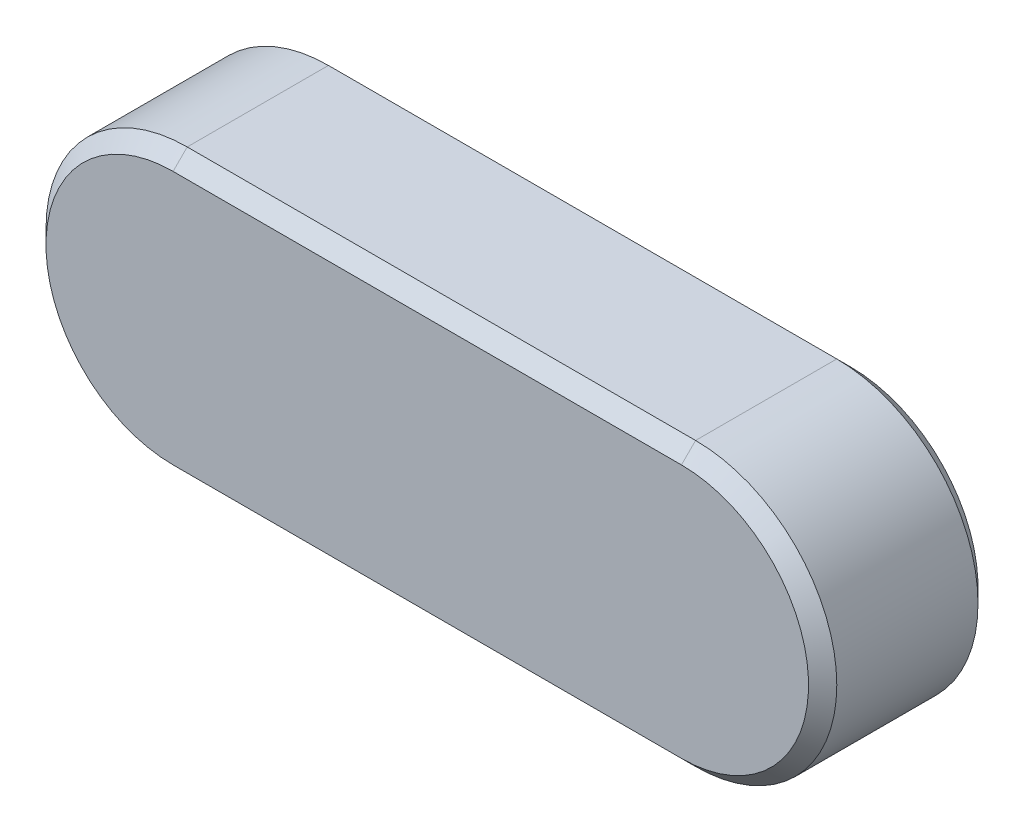
SolidWorks part; units mm, degrees
ref_plane "Front" through (0, 0, 0) normal (0, 0, 1) x (1, 0, 0)
ref_plane "Top" through (0, 0, 0) normal (0, 1, 0) x (1, 0, 0)
ref_plane "Right" through (0, 0, 0) normal (1, 0, 0) x (0, 0, -1)
sketch "Sketch1" plane through (0, 0, 0) normal (0, 0, 1) x (1, 0, 0)
  line L0 (0, 2.5) -> (-9, 2.5)
  line L1 (-9, -2.5) -> (0, -2.5)
  arc A0 (-9, 2.5) -> (-9, -2.5) centre (-9, 0) ccw
  arc A1 (0, -2.5) -> (0, 2.5) centre (0, 0) ccw
  dimension "b" = 5
  dimension "l" = 14
extrude "Extrude1" add sketch "Sketch1" along normal blind 3
sketch "Sketch2" plane through (0, 0, 0) normal (0, 0, 1) x (1, 0, 0)
  line L0 (0, 2.5) -> (-9, 2.5) construction
  line L1 (-11.5, 2.5) -> (2.5, 2.5)
  line L2 (-11.5, 2.5) -> (-11.5, -2.5)
  line L3 (-11.5, -2.5) -> (2.5, -2.5)
  line L4 (2.5, 2.5) -> (2.5, -2.5)
  line L5 (-9, -2.5) -> (0, -2.5) construction
  arc A0 (-9, 2.5) -> (-9, -2.5) centre (-9, 0) ccw construction
  arc A1 (0, -2.5) -> (0, 2.5) centre (0, 0) ccw construction
extrude "Extrude2" [suppressed] add sketch "Sketch2" along normal blind 3
sketch "Sketch3" plane through (0, 0, 0) normal (0, 0, 1) x (1, 0, 0)
  line L0 (-9, -2.5) -> (0, -2.5) construction
  line L1 (-9, -2.5) -> (2.5, -2.5)
  line L3 (-9, 2.5) -> (2.5, 2.5)
  line L4 (2.5, -2.5) -> (2.5, 2.5)
  arc A1 (-9, 2.5) -> (-9, -2.5) centre (-9, 0) ccw
  arc A2 (0, -2.5) -> (0, 2.5) centre (0, 0) ccw construction
  arc A3 (-9, 2.5) -> (-9, -2.5) centre (-9, 0) ccw construction
extrude "Extrude3" [suppressed] add sketch "Sketch3" along normal blind 3
chamfer "Chamfer1" distance 0.25 angle 45 8 edges at (-4.5, 2.5, 0) (-4.5, -2.5, 0) (-4.5, 2.5, 3) (-4.5, -2.5, 3) (-11.5, 0, 0) (-11.5, 0, 3) (2.5, 0, 0) (2.5, 0, 3)
equation "\"D1@Extrude2\" = \"h@Extrude1\""
equation "\"D1@Extrude3\" = \"h@Extrude1\""
